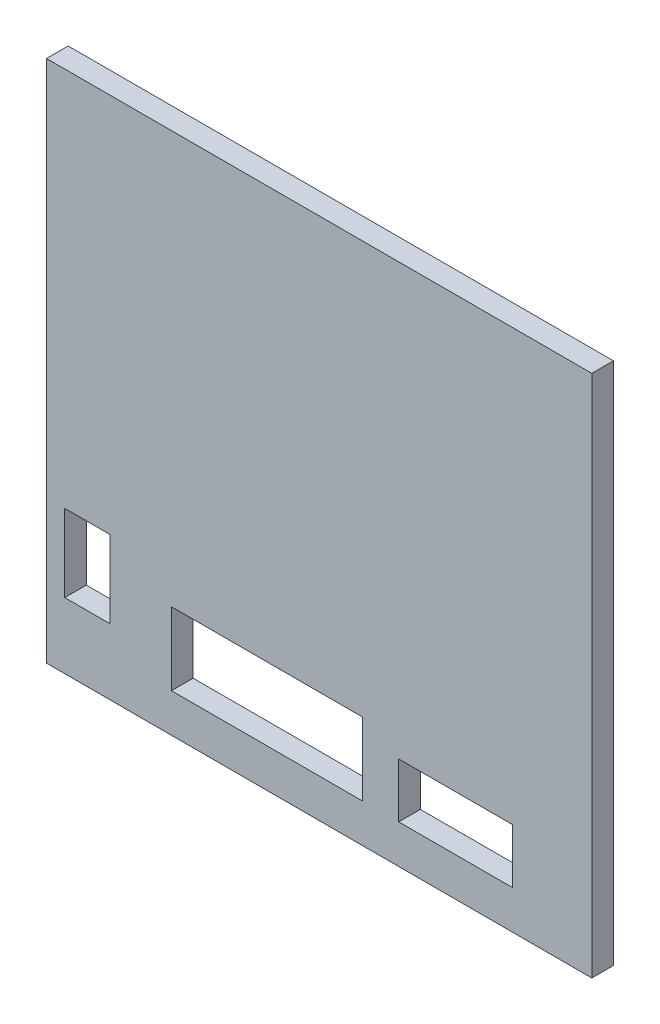
SolidWorks part; units mm, degrees
material "Oak"
ref_plane "Front Plane" through (0, 0, 0) normal (0, 0, 1) x (1, 0, 0)
ref_plane "Top Plane" through (0, 0, 0) normal (0, 1, 0) x (1, 0, 0)
ref_plane "Right Plane" through (0, 0, 0) normal (1, 0, 0) x (0, 0, -1)
sketch "Sketch1" plane through (0, 0, 0) normal (0, 0, 1) x (1, 0, 0)
  line L1 (-60, -57.6187) -> (60, -57.6187)
  line L2 (-60, -57.6187) -> (-60, 57.6188)
  line L3 (-60, 57.6188) -> (60, 57.6188)
  line L4 (60, -57.6187) -> (60, 57.6188)
  line L5 (-60, -57.6187) -> (60, 57.6188) construction
  line L6 (-60, 57.6188) -> (60, -57.6187) construction
  point P0 (0, 0)
  dimension "D1" = 120
  dimension "D2" = 115.2375
extrude "Boss-Extrude1" add sketch "Sketch1" against normal blind 4.7625
sketch "Sketch2" plane through (0, 0, 0) normal (0, 0, 1) x (1, 0, 0)
  line L0 (-60, 57.6188) -> (-60, -57.6187) construction
  line L1 (17.5, -37.1187) -> (42.5, -37.1187)
  line L2 (17.5, -37.1187) -> (17.5, -49.1187)
  line L3 (17.5, -49.1187) -> (42.5, -49.1187)
  line L4 (42.5, -37.1187) -> (42.5, -49.1187)
  line L5 (17.5, -37.1187) -> (42.5, -49.1187) construction
  line L6 (17.5, -49.1187) -> (42.5, -37.1187) construction
  line L7 (-32.5, -33.1187) -> (9.5, -33.1188)
  line L8 (-32.5, -33.1187) -> (-32.5, -49.1187)
  line L9 (-32.5, -49.1187) -> (9.5, -49.1187)
  line L10 (9.5, -33.1188) -> (9.5, -49.1187)
  line L11 (-32.5, -33.1187) -> (9.5, -49.1187) construction
  line L12 (-32.5, -49.1187) -> (9.5, -33.1188) construction
  line L13 (-56, -26.1188) -> (-46, -26.1188)
  line L14 (-56, -26.1188) -> (-56, -43.1188)
  line L15 (-56, -43.1188) -> (-46, -43.1188)
  line L16 (-46, -26.1188) -> (-46, -43.1188)
  line L17 (-56, -26.1188) -> (-46, -43.1188) construction
  line L18 (-56, -43.1188) -> (-46, -26.1188) construction
  line L20 (-60, -57.6187) -> (60, -57.6187) construction
  point P0 (30, -43.1187)
  point P5 (-11.5, -41.1187)
  point P10 (-51, -34.6187)
  dimension "D1" = 12
  dimension "D2" = 25
  dimension "D3" = 42
  dimension "D4" = 16
  dimension "D5" = 17
  dimension "D6" = 10
  dimension "D7" = 62.5
  dimension "D8" = 9
  dimension "D9" = 14.5
  dimension "D10" = 18.5
  dimension "D11" = 14.5
extrude "Cut-Extrude1" cut sketch "Sketch2" against normal through all
